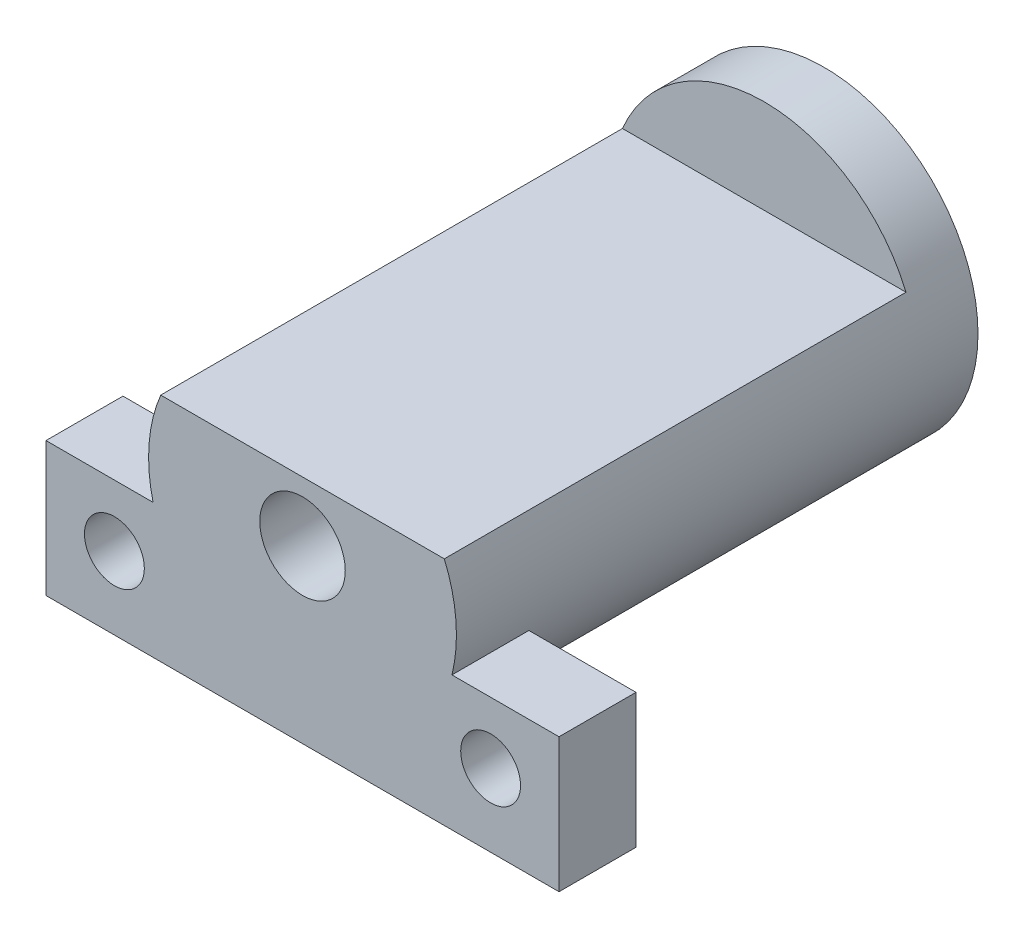
SolidWorks part; units mm, degrees
ref_plane "Front Plane" through (0, 0, 0) normal (0, 0, 1) x (1, 0, 0)
ref_plane "Top Plane" through (0, 0, 0) normal (0, 1, 0) x (1, 0, 0)
ref_plane "Right Plane" through (0, 0, 0) normal (1, 0, 0) x (0, 0, -1)
sketch "Sketch1" plane through (0, 0, 0) normal (0, 0, 1) x (1, 0, 0)
  circle A0 centre (0, 0) radius 18
  dimension "D1" = 36
extrude "Boss-Extrude1" add sketch "Sketch1" along normal blind 61
sketch "Sketch2" plane through (0, 0, 61) normal (0, 0, 1) x (1, 0, 0)
  line L1 (-17.2898, 21.1304) -> (22.2392, 21.1304)
  line L2 (-17.2898, 21.1304) -> (-17.2898, 7)
  line L3 (-17.2898, 7) -> (22.2392, 7)
  line L4 (22.2392, 21.1304) -> (22.2392, 7)
  circle A0 centre (0, 0) radius 18 construction
  dimension "D1" = 7
extrude "Cut-Extrude1" cut sketch "Sketch2" against normal blind 54
sketch "Sketch3" plane through (0, 0, 61) normal (0, 0, 1) x (1, 0, 0)
  line L1 (-30, -4.3129) -> (30, -4.3129)
  line L2 (-30, -4.3129) -> (-30, -20.0129)
  line L3 (-30, -20.0129) -> (30, -20.0129)
  line L4 (30, -4.3129) -> (30, -20.0129)
  arc A0 (-16.5831, 7) -> (16.5831, 7) centre (0, 0) ccw construction
  dimension "D1" = 60
  dimension "D2" = 30
  dimension "D3" = 15.7
extrude "Boss-Extrude2" add sketch "Sketch3" against normal blind 9
sketch "Sketch4" plane through (0, 0, 52) normal (0, 0, -1) x (-1, 0, 0)
  line L0 (30, -20.0129) -> (-30, -20.0129) construction
  line L1 (-30, -20.0129) -> (-30, -4.3129) construction
  circle A0 centre (-22, -11.5129) radius 3.5
  dimension "D3" = 7
  dimension "D1" = 8.5
  dimension "D2" = 8
extrude "Cut-Extrude2" cut sketch "Sketch4" against normal blind 10
pattern_linear "LPattern1" count 2 spacing 44 along (-1, 0, 0) of "Cut-Extrude2"
sketch "Sketch6" plane through (0, 0, 0) normal (0, 0, -1) x (-1, 0, 0)
  circle A0 centre (0, 0) radius 5
  circle A1 centre (0, 0) radius 18 construction
extrude "Cut-Extrude3" cut sketch "Sketch6" against normal blind 100
